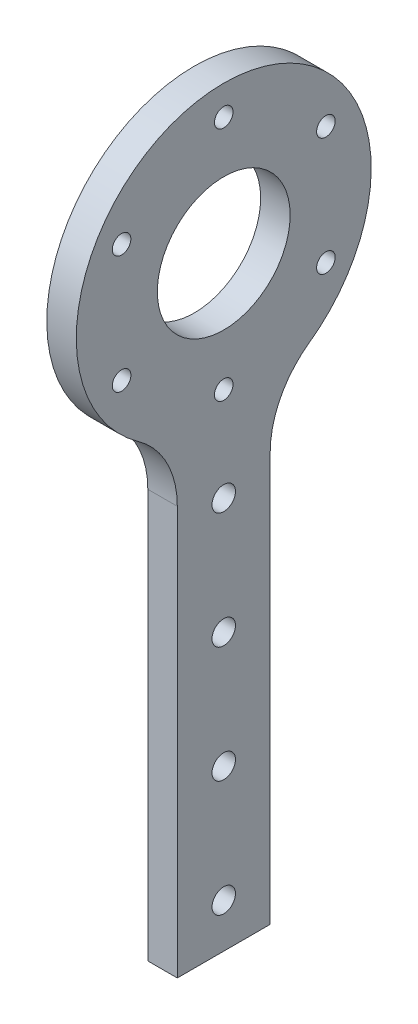
SolidWorks part; units mm, degrees
ref_plane "Front Plane" through (0, 0, 0) normal (0, 0, 1) x (1, 0, 0)
ref_plane "Top Plane" through (0, 0, 0) normal (0, 1, 0) x (1, 0, 0)
ref_plane "Right Plane" through (0, 0, 0) normal (1, 0, 0) x (0, 0, -1)
sketch "Sketch1" plane through (0, 0, 0) normal (1, 0, 0) x (0, 0, -1)
  line L0 (-10, -30.1341) -> (10, -30.1341) construction
  line L1 (-10, -30.1341) -> (-10, -130.1341)
  line L2 (-10, -130.1341) -> (10, -130.1341)
  line L3 (10, -130.1341) -> (10, -30.1341)
  arc A1 (10, -30.1341) -> (-10, -30.1341) centre (0, 0) ccw
  point P7 (0, -30.1341)
  dimension "D1" = 31.75
  dimension "D3" = 100
extrude "Boss-Extrude1" add sketch "Sketch1" along normal blind 6.35 contours A1 L0 | L0 L1 L2 L3
fillet "Fillet1" radius 20 2 edges at (3.175, -30.1341, -10) (3.175, -30.1341, 10)
sketch "Sketch2" plane through (6.35, 0, 0) normal (1, 0, 0) x (0, 0, -1)
  circle A0 centre (0, 0) radius 14.3
  circle A1 centre (0, 25.4) radius 2
  circle A2 centre (21.997, 12.7) radius 2
  circle A3 centre (21.997, -12.7) radius 2
  circle A4 centre (0, -25.4) radius 2
  circle A5 centre (-21.997, -12.7) radius 2
  circle A6 centre (-21.997, 12.7) radius 2
  point P18 (0, 0)
  dimension "D1" = 28.6
  dimension "D2" = 4
  dimension "D3" = 25.4
  dimension "D4" = 6
extrude "Cut-Extrude1" cut sketch "Sketch2" against normal through all
sketch "Sketch3" plane through (6.35, 0, 0) normal (1, 0, 0) x (0, 0, -1)
  circle A0 centre (0, -120.6366) radius 2.525
  circle A1 centre (0, -95.6366) radius 2.525
  circle A2 centre (0, -70.6366) radius 2.525
  circle A3 centre (0, -45.6366) radius 2.525
  dimension "D1" = 5.05
  dimension "D2" = 5.05
  dimension "D3" = 5.05
  dimension "D4" = 5.05
  dimension "D5" = 25
  dimension "D6" = 25
  dimension "D7" = 25
extrude "Cut-Extrude2" cut sketch "Sketch3" against normal through all
